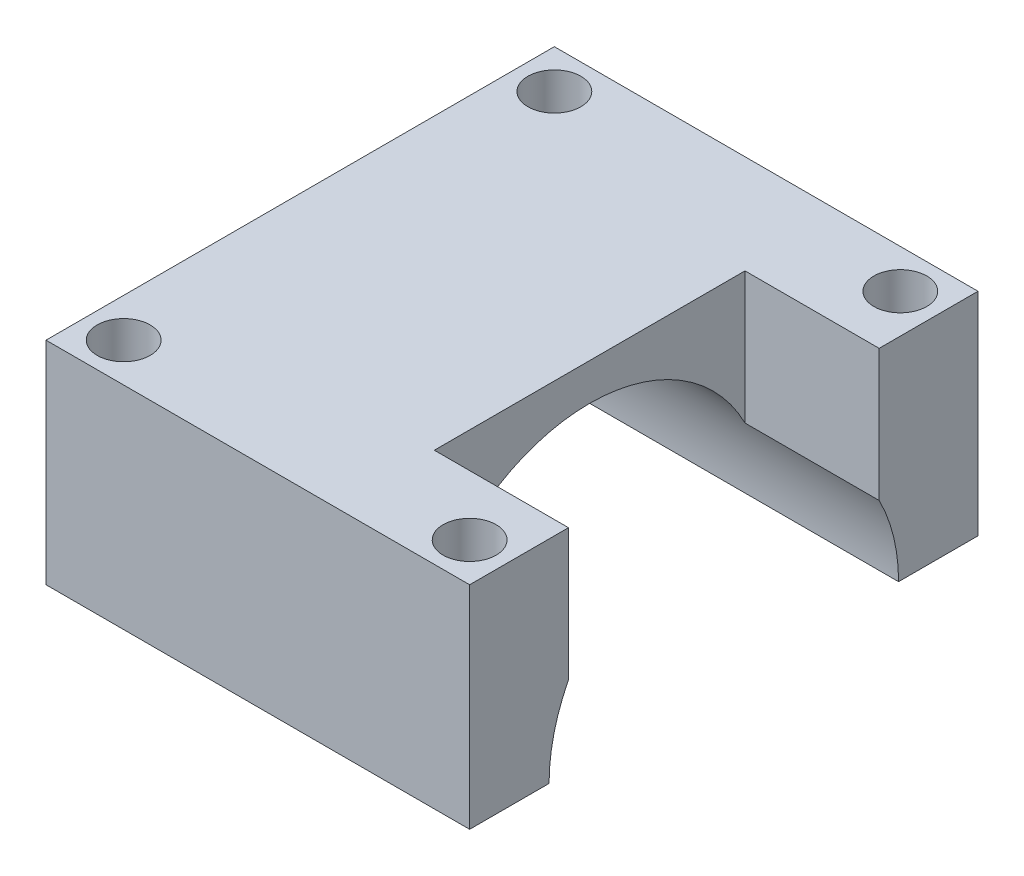
SolidWorks part; units mm, degrees
ref_plane "Front Plane" through (0, 0, 0) normal (0, 0, 1) x (1, 0, 0)
ref_plane "Top Plane" through (0, 0, 0) normal (0, 1, 0) x (1, 0, 0)
ref_plane "Right Plane" through (0, 0, 0) normal (1, 0, 0) x (0, 0, -1)
sketch "Sketch1" plane through (0, 0, 0) normal (0, 1, 0) x (1, 0, 0)
  line L1 (-15, -18) -> (15, -18)
  line L2 (-15, -18) -> (-15, 18)
  line L3 (-15, 18) -> (15, 18)
  line L4 (15, -18) -> (15, 18)
  line L5 (-15, -18) -> (15, 18) construction
  line L6 (-15, 18) -> (15, -18) construction
  point P0 (0, 0)
  dimension "D1" = 30
  dimension "D2" = 36
extrude "Boss-Extrude1" add sketch "Sketch1" along normal blind 30
sketch "Sketch3" plane through (15, 0, 0) normal (1, 0, 0) x (0, 0, -1)
  line L0 (0, 0) -> (0, 30) construction
  line L1 (-18, 0) -> (18, 0) construction
  line L2 (-18, 30) -> (18, 30) construction
  circle A0 centre (0, 15) radius 12.375
  dimension "D1" = 24.75
extrude "Cut-Extrude1" cut sketch "Sketch3" against normal blind 40
sketch "Sketch5" plane through (0, 30, 0) normal (0, 1, 0) x (1, 0, 0)
  line L7 (15, 18) -> (-15, 18) construction
  line L9 (-15, 18) -> (-15, -18) construction
  line L10 (0, 0) -> (0, 2.7791) construction
  line L11 (0, 2.7791) -> (0, 0) construction
  line L12 (0, 0) -> (-2.7536, 0) construction
  circle A1 centre (-12.25, 15.25) radius 1.875
  circle A2 centre (-12.25, -15.25) radius 1.875
  circle A3 centre (12.25, -15.25) radius 1.875
  circle A4 centre (12.25, 15.25) radius 1.875
  point P0 (0, 0)
  dimension "D2" = 3.75
  dimension "D3" = 2.75
  dimension "D4" = 2.75
extrude "Cut-Extrude2" cut sketch "Sketch5" against normal blind 40
sketch "Sketch7" plane through (0, 0, 0) normal (1, 0, 0) x (0, 0, -1)
  line L0 (-18, 30) -> (-18, 0) construction
  line L1 (-18, 15) -> (18, 15)
  line L2 (-18, 15) -> (-18, 0)
  line L3 (-18, 0) -> (18, 0)
  line L4 (18, 15) -> (18, 0)
extrude "Cut-Extrude3" cut sketch "Sketch7" against normal through all from surface at 15 starting at face at (15, 15, -12.375)
sketch "Sketch8" plane through (0, 30, 0) normal (0, 1, 0) x (1, 0, 0)
  line L0 (15, -18) -> (15, 18) construction
  line L2 (5.5, -11) -> (5.5, 11)
  line L5 (5.5, -11) -> (15, 0) construction
  line L6 (5.5, 11) -> (15, 0) construction
  line L7 (15, 11) -> (15, -11)
  line L8 (5.5, 11) -> (15, 11)
  line L9 (5.5, -11) -> (15, -11)
  point P0 (15, 0)
  dimension "D1" = 22
  dimension "D2" = 9.5
extrude "Cut-Extrude4" cut sketch "Sketch8" against normal blind 10
